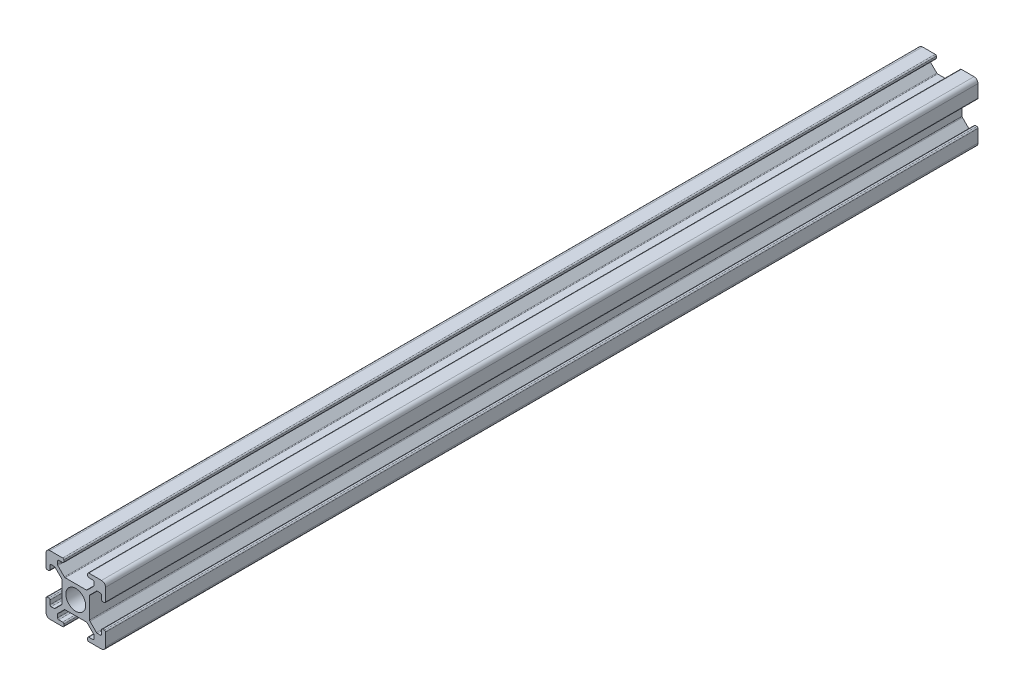
SolidWorks part; units mm, degrees
ref_plane "Front Plane" through (0, 0, 0) normal (0, 0, 1) x (1, 0, 0)
ref_plane "Top Plane" through (0, 0, 0) normal (0, 1, 0) x (1, 0, 0)
ref_plane "Right Plane" through (0, 0, 0) normal (1, 0, 0) x (0, 0, -1)
sketch "Sketch1" plane through (0, 0, 0) normal (0, 0, 1) x (1, 0, 0)
  line L0 (0.9971, -0.011) -> (4.1971, -0.011)
  line L1 (14.9971, 0.989) -> (14.9971, 4.189)
  line L2 (13.9971, 14.989) -> (10.7971, 14.989)
  line L3 (-0.0029, 13.989) -> (-0.0029, 10.789)
  line L4 (4.4971, 0.289) -> (4.4971, 0.689)
  line L5 (10.4971, 0.289) -> (10.4971, 0.689)
  line L6 (4.4971, 14.689) -> (4.4971, 14.289)
  line L7 (10.4971, 14.689) -> (10.4971, 14.289)
  line L8 (4.1971, 14.989) -> (0.9971, 14.989)
  line L9 (10.7971, -0.011) -> (13.9971, -0.011)
  line L10 (0.9971, 4.189) -> (0.9971, 3.189)
  line L11 (0.9971, 10.789) -> (0.9971, 11.7902)
  line L12 (14.6971, 10.5) -> (14.3, 10.5)
  line L13 (14.6971, 4.489) -> (14.3053, 4.489)
  line L14 (0.2971, 4.489) -> (0.6971, 4.489)
  line L15 (0.2971, 10.489) -> (0.6971, 10.489)
  line L16 (-0.0029, 4.189) -> (-0.0029, 0.989)
  line L17 (14.9971, 10.8) -> (14.9971, 13.989)
  line L18 (14, 10.8) -> (14, 11.8)
  line L19 (14.0053, 4.189) -> (14.0053, 3.189)
  line L20 (4.8302, 10.985) -> (10.1675, 10.985)
  line L21 (10.9699, 10.1634) -> (10.9699, 4.8261)
  line L22 (10.1715, 3.9947) -> (4.8343, 3.9947)
  line L23 (4.0029, 4.8261) -> (4.0029, 10.1634)
  line L24 (4.1971, 13.989) -> (3.1971, 13.989)
  line L25 (10.7971, 13.989) -> (11.7988, 13.989)
  line L26 (4.1971, 0.989) -> (3.1971, 0.989)
  line L27 (10.7971, 0.989) -> (11.8086, 0.989)
  line L28 (1.2971, 12.0902) -> (2.0579, 12.0902)
  line L29 (2.8971, 13.689) -> (2.8971, 12.9204)
  line L30 (1.2971, 2.889) -> (2.0658, 2.889)
  line L31 (2.8971, 1.289) -> (2.8971, 2.0576)
  line L32 (4.6181, 11.0728) -> (2.9867, 12.7042)
  line L33 (3.9121, 10.3808) -> (2.2729, 12.0018)
  line L34 (10.3796, 11.0728) -> (12.011, 12.7042)
  line L35 (11.0879, 10.3808) -> (12.7192, 12.0121)
  line L36 (11.0891, 4.6099) -> (12.7204, 2.9786)
  line L37 (10.3877, 3.9052) -> (12.0191, 2.2738)
  line L38 (4.6181, 3.9052) -> (2.9867, 2.2738)
  line L39 (3.9133, 4.6099) -> (2.282, 2.9786)
  line L40 (12.0988, 13.689) -> (12.0988, 12.9163)
  line L41 (13.7, 12.1) -> (12.9314, 12.1)
  line L42 (13.7053, 2.889) -> (12.9366, 2.889)
  line L43 (12.1086, 1.289) -> (12.1086, 2.0576)
  circle A0 centre (7.5, 7.5) radius 2.5
  arc A1 (0.9971, -0.011) -> (-0.0029, 0.989) centre (0.9971, 0.989) cw
  arc A2 (13.9971, -0.011) -> (14.9971, 0.989) centre (13.9971, 0.989) ccw
  arc A3 (14.9971, 13.989) -> (13.9971, 14.989) centre (13.9971, 13.989) ccw
  arc A4 (0.9971, 14.989) -> (-0.0029, 13.989) centre (0.9971, 13.989) ccw
  arc A5 (10.4971, 0.289) -> (10.7971, -0.011) centre (10.7971, 0.289) ccw
  arc A6 (10.4971, 0.689) -> (10.7971, 0.989) centre (10.7971, 0.689) cw
  arc A7 (4.4971, 0.289) -> (4.1971, -0.011) centre (4.1971, 0.289) cw
  arc A8 (4.4971, 0.689) -> (4.1971, 0.989) centre (4.1971, 0.689) ccw
  arc A9 (0.6971, 4.489) -> (0.9971, 4.189) centre (0.6971, 4.189) cw
  arc A10 (0.2971, 4.489) -> (-0.0029, 4.189) centre (0.2971, 4.189) ccw
  arc A11 (0.6971, 10.489) -> (0.9971, 10.789) centre (0.6971, 10.789) ccw
  arc A12 (0.2971, 10.489) -> (-0.0029, 10.789) centre (0.2971, 10.789) cw
  arc A13 (4.4971, 14.289) -> (4.1971, 13.989) centre (4.1971, 14.289) cw
  arc A14 (4.1971, 14.989) -> (4.4971, 14.689) centre (4.1971, 14.689) cw
  arc A15 (10.4971, 14.289) -> (10.7971, 13.989) centre (10.7971, 14.289) ccw
  arc A16 (10.7971, 14.989) -> (10.4971, 14.689) centre (10.7971, 14.689) ccw
  arc A17 (14.3053, 4.489) -> (14.0053, 4.189) centre (14.3053, 4.189) ccw
  arc A18 (14.9971, 4.189) -> (14.6971, 4.489) centre (14.6971, 4.189) ccw
  arc A19 (14.3, 10.5) -> (14, 10.8) centre (14.3, 10.8) cw
  arc A20 (14.9971, 10.8) -> (14.6971, 10.5) centre (14.6971, 10.8) cw
  arc A21 (11.7988, 13.989) -> (12.0988, 13.689) centre (11.7988, 13.689) cw
  arc A22 (14, 11.8) -> (13.7, 12.1) centre (13.7, 11.8) ccw
  arc A23 (14.0053, 3.189) -> (13.7053, 2.889) centre (13.7053, 3.189) cw
  arc A24 (11.8086, 0.989) -> (12.1086, 1.289) centre (11.8086, 1.289) ccw
  arc A25 (3.1971, 0.989) -> (2.8971, 1.289) centre (3.1971, 1.289) cw
  arc A26 (0.9971, 3.189) -> (1.2971, 2.889) centre (1.2971, 3.189) ccw
  arc A27 (0.9971, 11.7902) -> (1.2971, 12.0902) centre (1.2971, 11.7902) cw
  arc A28 (3.1971, 13.989) -> (2.8971, 13.689) centre (3.1971, 13.689) ccw
  arc A29 (10.3796, 11.0728) -> (10.1675, 10.985) centre (10.1675, 11.285) cw
  arc A30 (12.0988, 12.9163) -> (12.011, 12.7042) centre (11.7988, 12.9163) cw
  arc A31 (4.6181, 11.0728) -> (4.8302, 10.985) centre (4.8302, 11.285) ccw
  arc A32 (12.9314, 12.1) -> (12.7192, 12.0121) centre (12.9314, 11.8) ccw
  arc A33 (10.9699, 10.1634) -> (11.0879, 10.3808) centre (11.2692, 10.1417) cw
  arc A34 (11.0891, 4.6099) -> (10.9699, 4.8261) centre (11.269, 4.85) cw
  arc A35 (12.9366, 2.889) -> (12.7204, 2.9786) centre (12.9366, 3.1947) cw
  arc A36 (12.1086, 2.0576) -> (12.0191, 2.2738) centre (11.8029, 2.0576) ccw
  arc A37 (2.8971, 2.0576) -> (2.9867, 2.2738) centre (3.2029, 2.0576) cw
  arc A38 (10.3877, 3.9052) -> (10.1715, 3.9947) centre (10.1715, 3.689) ccw
  arc A39 (4.6181, 3.9052) -> (4.8343, 3.9947) centre (4.8343, 3.689) cw
  arc A40 (2.0658, 2.889) -> (2.282, 2.9786) centre (2.0658, 3.1947) ccw
  arc A41 (3.9133, 4.6099) -> (4.0029, 4.8261) centre (3.6971, 4.8261) ccw
  arc A42 (3.9121, 10.3808) -> (4.0029, 10.1634) centre (3.6971, 10.1634) cw
  arc A43 (2.8971, 12.9204) -> (2.9867, 12.7042) centre (3.2029, 12.9204) ccw
  arc A44 (2.0579, 12.0902) -> (2.2729, 12.0018) centre (2.0579, 11.7845) cw
extrude "Boss-Extrude1" add sketch "Sketch1" along normal blind 220
